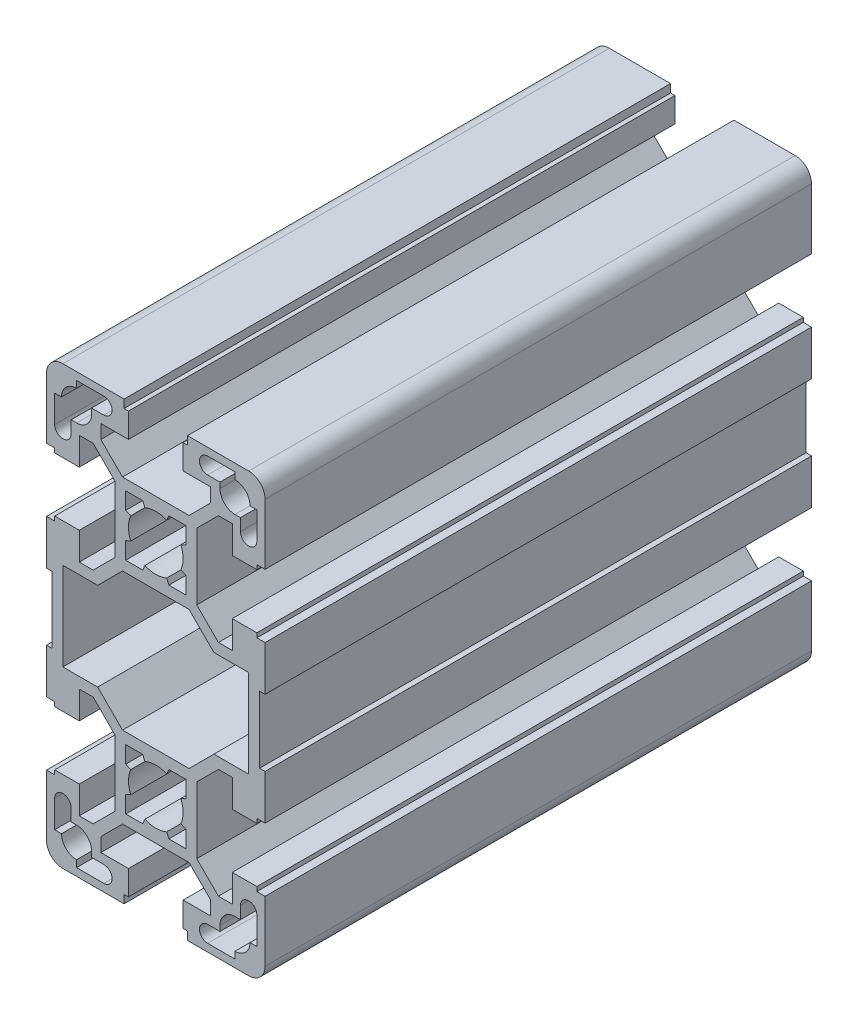
SolidWorks part; units mm, degrees
ref_plane "Front Plane" through (0, 0, 0) normal (0, 0, 1) x (1, 0, 0)
ref_plane "Top Plane" through (0, 0, 0) normal (0, 1, 0) x (1, 0, 0)
ref_plane "Right Plane" through (0, 0, 0) normal (1, 0, 0) x (0, 0, -1)
sketch "Sketch1" plane through (0, 0, 0) normal (0, 0, 1) x (1, 0, 0)
  line L0 (10.6358, -8.0584) -> (17, -8.0584)
  line L1 (19, -6.1084) -> (20, -6.1084)
  line L2 (19, 6.1084) -> (19, -6.1084)
  line L3 (-10.05, -34) -> (-10.05, -31.4642)
  line L4 (-18.5, -34.6084) -> (-18.5, -29.6084)
  line L5 (-20, -25.9084) -> (-20, -37)
  line L6 (17, -8.0584) -> (17, 8.0584)
  line L7 (5.5, -14.6084) -> (2.3979, -14.6084)
  line L8 (-17, -40) -> (-5.8, -40)
  line L9 (-5, -34) -> (-10.05, -34)
  line L10 (-11.75, -34.6084) -> (-11.75, -35.6084)
  line L11 (-11.75, -35.6084) -> (-9.5, -35.6084)
  line L12 (-9.5, -38.6084) -> (-14.5, -38.6084)
  line L13 (-14.5, -38.6084) -> (-14.5, -37.3584)
  line L14 (-17.25, -34.6084) -> (-18.5, -34.6084)
  line L15 (4.5833, -18.1101) -> (5.5, -17.7105)
  line L16 (-5.8, -40) -> (-5.8, -38.5)
  line L17 (-5.8, -38.5) -> (-5, -38.5)
  line L18 (-5, -38.5) -> (-5, -34)
  line L19 (2.3979, -14.6084) -> (1.9983, -15.5251)
  line L20 (5.5, -17.7105) -> (5.5, -14.6084)
  line L21 (18.5, -15.1084) -> (14, -15.1084)
  line L22 (18.5, -14.3084) -> (18.5, -15.1084)
  line L23 (14, -10.0584) -> (11.4642, -10.0584)
  line L24 (14, -15.1084) -> (14, -10.0584)
  line L25 (20, -14.3084) -> (18.5, -14.3084)
  line L26 (0, 44.6651) -> (0, -44.6651) construction
  line L27 (11.4642, -10.0584) -> (7.5, -14.0226)
  line L28 (5.5, -25.6084) -> (5.5, -22.5063)
  line L29 (2.3979, -25.6084) -> (5.5, -25.6084)
  line L30 (1.9983, -24.6917) -> (2.3979, -25.6084)
  line L31 (5.5, -22.5063) -> (4.5833, -22.1067)
  line L32 (14, -25.1084) -> (18.5, -25.1084)
  line L33 (18.5, -25.1084) -> (18.5, -25.9084)
  line L34 (18.5, -25.9084) -> (20, -25.9084)
  line L35 (11.4642, -30.1584) -> (14, -30.1584)
  line L36 (15.5, -31.8584) -> (14.5, -31.8584)
  line L37 (15.5, -29.6084) -> (15.5, -31.8584)
  line L38 (14, -30.1584) -> (14, -25.1084)
  line L39 (-20, -6.1084) -> (-20, -14.3084)
  line L40 (-6.0858, -12.6084) -> (-10.6358, -8.0584)
  line L41 (-7.5, -14.0226) -> (-7.5, -26.1942)
  line L42 (10.05, -31.4642) -> (6.0858, -27.5)
  line L43 (-7.5, -26.1942) -> (-11.4642, -30.1584)
  line L44 (-10.05, -31.4642) -> (-6.0858, -27.5)
  line L45 (-14, -30.1584) -> (-14, -25.1084)
  line L46 (-15.5, -29.6084) -> (-15.5, -31.8584)
  line L47 (-15.5, -31.8584) -> (-14.5, -31.8584)
  line L48 (-11.4642, -30.1584) -> (-14, -30.1584)
  line L49 (-18.5, -25.9084) -> (-20, -25.9084)
  line L50 (-18.5, -25.1084) -> (-18.5, -25.9084)
  line L51 (-14, -25.1084) -> (-18.5, -25.1084)
  line L52 (7.5, -26.1942) -> (11.4642, -30.1584)
  line L53 (-6.0858, -27.5) -> (6.0858, -27.5)
  line L54 (7.5, -14.0226) -> (7.5, -26.1942)
  line L55 (-5.5, -22.5063) -> (-4.5833, -22.1067)
  line L56 (-1.9983, -24.6917) -> (-2.3979, -25.6084)
  line L57 (-2.3979, -25.6084) -> (-5.5, -25.6084)
  line L58 (-5.5, -25.6084) -> (-5.5, -22.5063)
  line L59 (6.0858, -12.6084) -> (10.6358, -8.0584)
  line L60 (20, -6.1084) -> (20, -14.3084)
  line L61 (5, -38.5) -> (5, -34)
  line L62 (5.8, -38.5) -> (5, -38.5)
  line L63 (-11.4642, -10.0584) -> (-7.5, -14.0226)
  line L64 (-20, -14.3084) -> (-18.5, -14.3084)
  line L65 (-14, -15.1084) -> (-14, -10.0584)
  line L66 (-14, -10.0584) -> (-11.4642, -10.0584)
  line L67 (-18.5, -14.3084) -> (-18.5, -15.1084)
  line L68 (-18.5, -15.1084) -> (-14, -15.1084)
  line L69 (5.8, -40) -> (5.8, -38.5)
  line L70 (-5.5, -17.7105) -> (-5.5, -14.6084)
  line L71 (-2.3979, -14.6084) -> (-1.9983, -15.5251)
  line L72 (17.25, -34.6084) -> (18.5, -34.6084)
  line L73 (-4.5833, -18.1101) -> (-5.5, -17.7105)
  line L74 (14.5, -38.6084) -> (14.5, -37.3584)
  line L75 (6.0858, -12.6084) -> (-6.0858, -12.6084)
  line L76 (-5.5, -14.6084) -> (-2.3979, -14.6084)
  line L77 (9.5, -38.6084) -> (14.5, -38.6084)
  line L78 (11.75, -35.6084) -> (9.5, -35.6084)
  line L79 (-17, -8.0584) -> (-17, 8.0584)
  line L80 (-19, 6.1084) -> (-19, -6.1084)
  line L81 (-19, -6.1084) -> (-20, -6.1084)
  line L82 (-10.6358, -8.0584) -> (-17, -8.0584)
  line L83 (11.75, -34.6084) -> (11.75, -35.6084)
  line L84 (5, -34) -> (10.05, -34)
  line L85 (17, -40) -> (5.8, -40)
  line L86 (20, -25.9084) -> (20, -37)
  line L87 (18.5, -34.6084) -> (18.5, -29.6084)
  line L88 (10.05, -34) -> (10.05, -31.4642)
  line L89 (10.05, 34) -> (10.05, 31.4642)
  line L90 (18.5, 34.6084) -> (18.5, 29.6084)
  line L91 (20, 25.9084) -> (20, 37)
  line L92 (17, 40) -> (5.8, 40)
  line L93 (5, 34) -> (10.05, 34)
  line L94 (11.75, 34.6084) -> (11.75, 35.6084)
  line L95 (-10.6358, 8.0584) -> (-17, 8.0584)
  line L96 (-19, 6.1084) -> (-20, 6.1084)
  line L97 (11.75, 35.6084) -> (9.5, 35.6084)
  line L98 (9.5, 38.6084) -> (14.5, 38.6084)
  line L99 (-5.5, 14.6084) -> (-2.3979, 14.6084)
  line L100 (6.0858, 12.6084) -> (-6.0858, 12.6084)
  line L101 (14.5, 38.6084) -> (14.5, 37.3584)
  line L102 (-4.5833, 18.1101) -> (-5.5, 17.7105)
  line L103 (17.25, 34.6084) -> (18.5, 34.6084)
  line L104 (-2.3979, 14.6084) -> (-1.9983, 15.5251)
  line L105 (-5.5, 17.7105) -> (-5.5, 14.6084)
  line L106 (5.8, 40) -> (5.8, 38.5)
  line L107 (-18.5, 15.1084) -> (-14, 15.1084)
  line L108 (-18.5, 14.3084) -> (-18.5, 15.1084)
  line L109 (-14, 10.0584) -> (-11.4642, 10.0584)
  line L110 (-14, 15.1084) -> (-14, 10.0584)
  line L111 (-20, 14.3084) -> (-18.5, 14.3084)
  line L112 (-11.4642, 10.0584) -> (-7.5, 14.0226)
  line L113 (5.8, 38.5) -> (5, 38.5)
  line L114 (5, 38.5) -> (5, 34)
  line L115 (20, 6.1084) -> (20, 14.3084)
  line L116 (6.0858, 12.6084) -> (10.6358, 8.0584)
  line L117 (-5.5, 25.6084) -> (-5.5, 22.5063)
  line L118 (-2.3979, 25.6084) -> (-5.5, 25.6084)
  line L119 (-1.9983, 24.6917) -> (-2.3979, 25.6084)
  line L120 (-5.5, 22.5063) -> (-4.5833, 22.1067)
  line L121 (7.5, 14.0226) -> (7.5, 26.1942)
  line L122 (-6.0858, 27.5) -> (6.0858, 27.5)
  line L123 (7.5, 26.1942) -> (11.4642, 30.1584)
  line L124 (-14, 25.1084) -> (-18.5, 25.1084)
  line L125 (-18.5, 25.1084) -> (-18.5, 25.9084)
  line L126 (-18.5, 25.9084) -> (-20, 25.9084)
  line L127 (-11.4642, 30.1584) -> (-14, 30.1584)
  line L128 (-15.5, 31.8584) -> (-14.5, 31.8584)
  line L129 (-15.5, 29.6084) -> (-15.5, 31.8584)
  line L130 (-14, 30.1584) -> (-14, 25.1084)
  line L131 (-10.05, 31.4642) -> (-6.0858, 27.5)
  line L132 (-7.5, 26.1942) -> (-11.4642, 30.1584)
  line L133 (10.05, 31.4642) -> (6.0858, 27.5)
  line L134 (-7.5, 14.0226) -> (-7.5, 26.1942)
  line L135 (-6.0858, 12.6084) -> (-10.6358, 8.0584)
  line L136 (-20, 6.1084) -> (-20, 14.3084)
  line L137 (14, 30.1584) -> (14, 25.1084)
  line L138 (15.5, 29.6084) -> (15.5, 31.8584)
  line L139 (15.5, 31.8584) -> (14.5, 31.8584)
  line L140 (11.4642, 30.1584) -> (14, 30.1584)
  line L141 (18.5, 25.9084) -> (20, 25.9084)
  line L142 (18.5, 25.1084) -> (18.5, 25.9084)
  line L143 (14, 25.1084) -> (18.5, 25.1084)
  line L144 (5.5, 22.5063) -> (4.5833, 22.1067)
  line L145 (1.9983, 24.6917) -> (2.3979, 25.6084)
  line L146 (2.3979, 25.6084) -> (5.5, 25.6084)
  line L147 (5.5, 25.6084) -> (5.5, 22.5063)
  line L148 (11.4642, 10.0584) -> (7.5, 14.0226)
  line L149 (20, 14.3084) -> (18.5, 14.3084)
  line L150 (14, 15.1084) -> (14, 10.0584)
  line L151 (14, 10.0584) -> (11.4642, 10.0584)
  line L152 (18.5, 14.3084) -> (18.5, 15.1084)
  line L153 (18.5, 15.1084) -> (14, 15.1084)
  line L154 (5.5, 17.7105) -> (5.5, 14.6084)
  line L155 (2.3979, 14.6084) -> (1.9983, 15.5251)
  line L156 (-5, 38.5) -> (-5, 34)
  line L157 (-5.8, 38.5) -> (-5, 38.5)
  line L158 (-5.8, 40) -> (-5.8, 38.5)
  line L159 (4.5833, 18.1101) -> (5.5, 17.7105)
  line L160 (-17.25, 34.6084) -> (-18.5, 34.6084)
  line L161 (-14.5, 38.6084) -> (-14.5, 37.3584)
  line L162 (-9.5, 38.6084) -> (-14.5, 38.6084)
  line L163 (-11.75, 35.6084) -> (-9.5, 35.6084)
  line L164 (-11.75, 34.6084) -> (-11.75, 35.6084)
  line L165 (-5, 34) -> (-10.05, 34)
  line L166 (-17, 40) -> (-5.8, 40)
  line L167 (5.5, 14.6084) -> (2.3979, 14.6084)
  line L168 (-20, 25.9084) -> (-20, 37)
  line L169 (-18.5, 34.6084) -> (-18.5, 29.6084)
  line L170 (-10.05, 34) -> (-10.05, 31.4642)
  line L171 (19, 6.1084) -> (20, 6.1084)
  line L172 (10.6358, 8.0584) -> (17, 8.0584)
  line L175 (-39.3803, 0) -> (39.3803, 0) construction
  arc A0 (-11.75, -34.6084) -> (-14.5, -31.8584) centre (-14.5, -34.6084) ccw
  arc A1 (15.5, -29.6084) -> (18.5, -29.6084) centre (17, -29.6084) cw
  arc A2 (-9.5, -38.6084) -> (-9.5, -35.6084) centre (-9.5, -37.1084) ccw
  arc A3 (-20, -37) -> (-17, -40) centre (-17, -37) ccw
  arc A4 (-17.25, -34.6084) -> (-14.5, -37.3584) centre (-14.5, -34.6084) ccw
  arc A5 (4.5833, -18.1101) -> (4.5833, -22.1067) centre (0, -20.1084) cw
  arc A6 (17.25, -34.6084) -> (14.5, -37.3584) centre (14.5, -34.6084) cw
  arc A7 (20, -37) -> (17, -40) centre (17, -37) cw
  arc A8 (9.5, -38.6084) -> (9.5, -35.6084) centre (9.5, -37.1084) cw
  arc A9 (11.75, -34.6084) -> (14.5, -31.8584) centre (14.5, -34.6084) cw
  arc A10 (-4.5833, -18.1101) -> (-4.5833, -22.1067) centre (0, -20.1084) ccw
  arc A11 (-15.5, -29.6084) -> (-18.5, -29.6084) centre (-17, -29.6084) ccw
  arc A12 (-1.9983, -24.6917) -> (1.9983, -24.6917) centre (0, -20.1084) ccw
  arc A13 (1.9983, -15.5251) -> (-1.9983, -15.5251) centre (0, -20.1084) ccw
  arc A14 (1.9983, 15.5251) -> (-1.9983, 15.5251) centre (0, 20.1084) cw
  arc A15 (-1.9983, 24.6917) -> (1.9983, 24.6917) centre (0, 20.1084) cw
  arc A16 (-15.5, 29.6084) -> (-18.5, 29.6084) centre (-17, 29.6084) cw
  arc A17 (-4.5833, 18.1101) -> (-4.5833, 22.1067) centre (0, 20.1084) cw
  arc A18 (11.75, 34.6084) -> (14.5, 31.8584) centre (14.5, 34.6084) ccw
  arc A19 (9.5, 38.6084) -> (9.5, 35.6084) centre (9.5, 37.1084) ccw
  arc A20 (20, 37) -> (17, 40) centre (17, 37) ccw
  arc A21 (17.25, 34.6084) -> (14.5, 37.3584) centre (14.5, 34.6084) ccw
  arc A22 (4.5833, 18.1101) -> (4.5833, 22.1067) centre (0, 20.1084) ccw
  arc A23 (-17.25, 34.6084) -> (-14.5, 37.3584) centre (-14.5, 34.6084) cw
  arc A24 (-20, 37) -> (-17, 40) centre (-17, 37) cw
  arc A25 (-9.5, 38.6084) -> (-9.5, 35.6084) centre (-9.5, 37.1084) cw
  arc A26 (15.5, 29.6084) -> (18.5, 29.6084) centre (17, 29.6084) ccw
  arc A27 (-11.75, 34.6084) -> (-14.5, 31.8584) centre (-14.5, 34.6084) cw
  point P44 (0, -12.6084)
  point P77 (0, -27.5)
  point P143 (0, 27.5)
  point P144 (0, 12.6084)
  point P156 (-19, 0)
  point P157 (-17, 0)
  point P230 (17, 0)
  point P231 (19, 0)
  dimension "D3" = 10
  dimension "D1" = 40
  dimension "D2" = 80
  dimension "D4" = 10
  dimension "D5" = 10
extrude "Extrude1" add sketch "Sketch1" against normal blind 100
